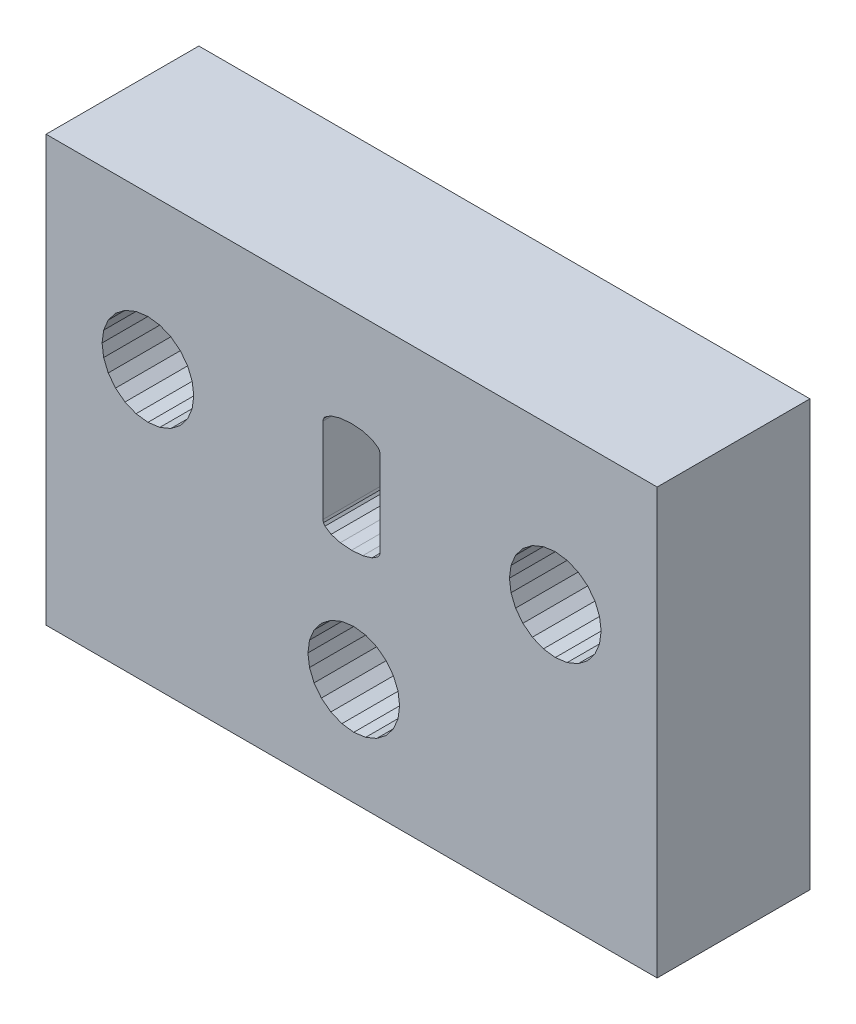
SolidWorks part; units mm, degrees
material "Maple"
ref_plane "Front Plane" through (0, 0, 0) normal (0, 0, 1) x (1, 0, 0)
ref_plane "Top Plane" through (0, 0, 0) normal (0, 1, 0) x (1, 0, 0)
ref_plane "Right Plane" through (0, 0, 0) normal (1, 0, 0) x (0, 0, -1)
sketch "Sketch1" plane through (0, 0, 0) normal (0, 0, 1) x (1, 0, 0)
  line L6932 (242.8989, 129.3069) -> (242.9602, 128.841)
  line L6933 (258.8978, 129.3069) -> (258.9591, 128.841)
  line L6934 (260.2319, 131.0456) -> (259.7978, 130.8657)
  line L6935 (244.6989, 127.5069) -> (245.1648, 127.5682)
  line L6936 (259.1389, 130.2069) -> (258.9591, 129.7728)
  line L6937 (244.233, 127.5682) -> (244.6989, 127.5069)
  line L6938 (245.1648, 131.0456) -> (244.6989, 131.1069)
  line L6939 (240.6989, 135.3069) -> (264.6989, 135.3069)
  line L6940 (240.6989, 118.6069) -> (240.6989, 135.3069)
  line L6941 (264.6989, 135.3069) -> (264.6989, 118.6069)
  line L6942 (264.6989, 118.6069) -> (240.6989, 118.6069)
  line L6943 (243.14, 130.2069) -> (242.9602, 129.7728)
  line L6944 (246.2577, 130.2069) -> (245.9717, 130.5797)
  line L6945 (259.7978, 127.748) -> (260.2319, 127.5682)
  line L6946 (259.7978, 130.8657) -> (259.425, 130.5797)
  line L6947 (262.2566, 130.2069) -> (261.9706, 130.5797)
  line L6948 (245.9717, 130.5797) -> (245.5989, 130.8657)
  line L6949 (245.5989, 130.8657) -> (245.1648, 131.0456)
  line L6950 (246.4376, 128.841) -> (246.4989, 129.3069)
  line L6951 (258.9591, 128.841) -> (259.1389, 128.4069)
  line L6952 (243.7989, 127.748) -> (244.233, 127.5682)
  line L6953 (246.4989, 129.3069) -> (246.4376, 129.7728)
  line L6954 (262.4978, 129.3069) -> (262.4364, 129.7728)
  line L6955 (261.9706, 130.5797) -> (261.5978, 130.8657)
  line L6956 (243.4261, 130.5797) -> (243.14, 130.2069)
  line L6957 (246.2577, 128.4069) -> (246.4376, 128.841)
  line L6958 (245.5989, 127.748) -> (245.9717, 128.0341)
  line L6959 (245.9717, 128.0341) -> (246.2577, 128.4069)
  line L6960 (260.2319, 127.5682) -> (260.6978, 127.5069)
  line L6961 (259.425, 130.5797) -> (259.1389, 130.2069)
  line L6962 (258.9591, 129.7728) -> (258.8978, 129.3069)
  line L6963 (261.5978, 130.8657) -> (261.1636, 131.0456)
  line L6964 (243.7989, 130.8657) -> (243.4261, 130.5797)
  line L6965 (261.9706, 128.0341) -> (262.2566, 128.4069)
  line L6966 (244.6989, 131.1069) -> (244.233, 131.0456)
  line L6967 (261.1636, 127.5682) -> (261.5978, 127.748)
  line L6968 (251.2248, 121.9069) -> (251.5109, 121.5341)
  line L6969 (251.045, 122.341) -> (251.2248, 121.9069)
  line L6970 (253.2495, 121.0682) -> (253.6836, 121.2481)
  line L6971 (254.5223, 123.2728) -> (254.3425, 123.7069)
  line L6972 (252.3178, 124.5456) -> (251.8836, 124.3657)
  line L6973 (251.045, 123.2728) -> (250.9836, 122.8069)
  line L6974 (259.1389, 128.4069) -> (259.425, 128.0341)
  line L6975 (259.425, 128.0341) -> (259.7978, 127.748)
  line L6976 (262.2566, 128.4069) -> (262.4364, 128.841)
  line L6977 (260.6978, 127.5069) -> (261.1636, 127.5682)
  line L6978 (262.4364, 129.7728) -> (262.2566, 130.2069)
  line L6979 (243.4261, 128.0341) -> (243.7989, 127.748)
  line L6980 (261.5978, 127.748) -> (261.9706, 128.0341)
  line L6981 (262.4364, 128.841) -> (262.4978, 129.3069)
  line L6982 (243.14, 128.4069) -> (243.4261, 128.0341)
  line L6983 (242.9602, 128.841) -> (243.14, 128.4069)
  line L6984 (251.8836, 121.2481) -> (252.3178, 121.0682)
  line L6985 (254.5836, 122.8069) -> (254.5223, 123.2728)
  line L6986 (251.5109, 124.0797) -> (251.2248, 123.7069)
  line L6987 (254.3425, 121.9069) -> (254.5223, 122.341)
  line L6988 (245.1648, 127.5682) -> (245.5989, 127.748)
  line L6989 (246.4376, 129.7728) -> (246.2577, 130.2069)
  line L6990 (244.233, 131.0456) -> (243.7989, 130.8657)
  line L6991 (261.1636, 131.0456) -> (260.6978, 131.1069)
  line L6992 (242.9602, 129.7728) -> (242.8989, 129.3069)
  line L6993 (260.6978, 131.1069) -> (260.2319, 131.0456)
  line L6994 (250.9836, 122.8069) -> (251.045, 122.341)
  line L6995 (251.2248, 123.7069) -> (251.045, 123.2728)
  line L6996 (251.8836, 124.3657) -> (251.5109, 124.0797)
  line L6997 (252.7836, 124.6069) -> (252.3178, 124.5456)
  line L6998 (253.2495, 124.5456) -> (252.7836, 124.6069)
  line L6999 (253.6836, 124.3657) -> (253.2495, 124.5456)
  line L7000 (254.0564, 124.0797) -> (253.6836, 124.3657)
  line L7001 (254.3425, 123.7069) -> (254.0564, 124.0797)
  line L7002 (254.5223, 122.341) -> (254.5836, 122.8069)
  line L7003 (254.0564, 121.5341) -> (254.3425, 121.9069)
  line L7004 (253.6836, 121.2481) -> (254.0564, 121.5341)
  line L7005 (252.7836, 121.0069) -> (253.2495, 121.0682)
  line L7006 (252.3178, 121.0682) -> (252.7836, 121.0069)
  line L7007 (251.5109, 121.5341) -> (251.8836, 121.2481)
  line L9434 (251.5714, 127.6358) -> (251.5915, 127.5397)
  line L9435 (251.5915, 127.5397) -> (251.6517, 127.4509)
  line L9436 (251.6517, 127.4509) -> (251.8929, 127.2956)
  line L9437 (251.8929, 127.2956) -> (252.2543, 127.1902)
  line L9438 (252.2543, 127.1902) -> (252.6953, 127.1551)
  line L9439 (252.6953, 127.1551) -> (253.1363, 127.1902)
  line L9440 (253.1363, 127.1902) -> (253.4976, 127.2956)
  line L9441 (253.4976, 127.2956) -> (253.7388, 127.4509)
  line L9442 (253.7388, 127.4509) -> (253.7991, 127.5397)
  line L9443 (253.7991, 127.5397) -> (253.8192, 127.6358)
  line L9444 (253.8192, 127.6358) -> (253.8192, 130.9823)
  line L9445 (253.8192, 130.9823) -> (253.7991, 131.0785)
  line L9446 (253.7991, 131.0785) -> (253.7388, 131.1672)
  line L9447 (253.7388, 131.1672) -> (253.4976, 131.3225)
  line L9448 (253.4976, 131.3225) -> (253.1363, 131.4279)
  line L9449 (253.1363, 131.4279) -> (252.6953, 131.463)
  line L9450 (252.6953, 131.463) -> (252.2543, 131.4279)
  line L9451 (252.2543, 131.4279) -> (251.8929, 131.3225)
  line L9452 (251.8929, 131.3225) -> (251.6517, 131.1672)
  line L9453 (251.6517, 131.1672) -> (251.5915, 131.0785)
  line L9454 (251.5915, 131.0785) -> (251.5714, 130.9823)
  line L9455 (251.5714, 130.9823) -> (251.5714, 127.6358)
  line L9456 (253.8192, 127.6358) -> (253.7991, 127.5397)
  line L9457 (253.7991, 127.5397) -> (253.7388, 127.4509)
  line L9458 (253.7388, 127.4509) -> (253.4976, 127.2956)
  line L9459 (253.4976, 127.2956) -> (253.1363, 127.1902)
  line L9460 (253.1363, 127.1902) -> (252.6953, 127.1551)
  line L9461 (252.6953, 127.1551) -> (252.2543, 127.1902)
  line L9462 (252.2543, 127.1902) -> (251.8929, 127.2956)
  line L9463 (251.8929, 127.2956) -> (251.6517, 127.4509)
  line L9464 (251.6517, 127.4509) -> (251.5915, 127.5397)
  line L9465 (251.5915, 127.5397) -> (251.5714, 127.6358)
  line L9466 (251.5714, 127.6358) -> (251.5714, 130.9823)
  line L9467 (251.5714, 130.9823) -> (251.5915, 131.0785)
  line L9468 (251.5915, 131.0785) -> (251.6517, 131.1672)
  line L9469 (251.6517, 131.1672) -> (251.8929, 131.3225)
  line L9470 (251.8929, 131.3225) -> (252.2543, 131.4279)
  line L9471 (252.2543, 131.4279) -> (252.6953, 131.463)
  line L9472 (252.6953, 131.463) -> (253.1363, 131.4279)
  line L9473 (253.1363, 131.4279) -> (253.4976, 131.3225)
  line L9474 (253.4976, 131.3225) -> (253.7388, 131.1672)
  line L9475 (253.7388, 131.1672) -> (253.7991, 131.0785)
  line L9476 (253.7991, 131.0785) -> (253.8192, 130.9823)
  line L9477 (253.8192, 130.9823) -> (253.8192, 127.6358)
extrude "Boss-Extrude1" add sketch "Sketch1" along normal blind 6 contours L6942 L6941 L6939 L6940 L9455 L9454 L9453 L9452 L9451 L9450 L9449 L9448 L9447 L9446 L9445 L9444 L9443 L9442 L9441 L9440 L9439 L9438 L9437 L9436 L9435 L9434 L7007 L6968 L6969 L6994 L6973 L6995 L6986 L6996 L6972 L6997 L6998 L6999 L7000 L7001 L6971 L6985 L7002 L6987 L7003 L7004 L6970 L7005 L7006
